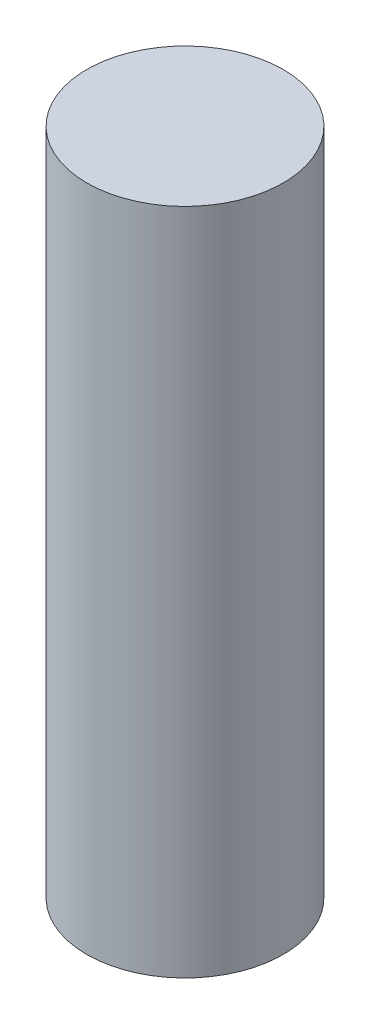
SolidWorks part; units mm, degrees
ref_plane "Front Plane" through (0, 0, 0) normal (0, 0, 1) x (1, 0, 0)
ref_plane "Top Plane" through (0, 0, 0) normal (0, 1, 0) x (1, 0, 0)
ref_plane "Right Plane" through (0, 0, 0) normal (1, 0, 0) x (0, 0, -1)
sketch "Sketch1" plane through (0, 0, 0) normal (0, 1, 0) x (1, 0, 0)
  circle A0 centre (0, 0) radius 5
  dimension "D1" = 10
extrude "Boss-Extrude1" add sketch "Sketch1" along normal blind 34
